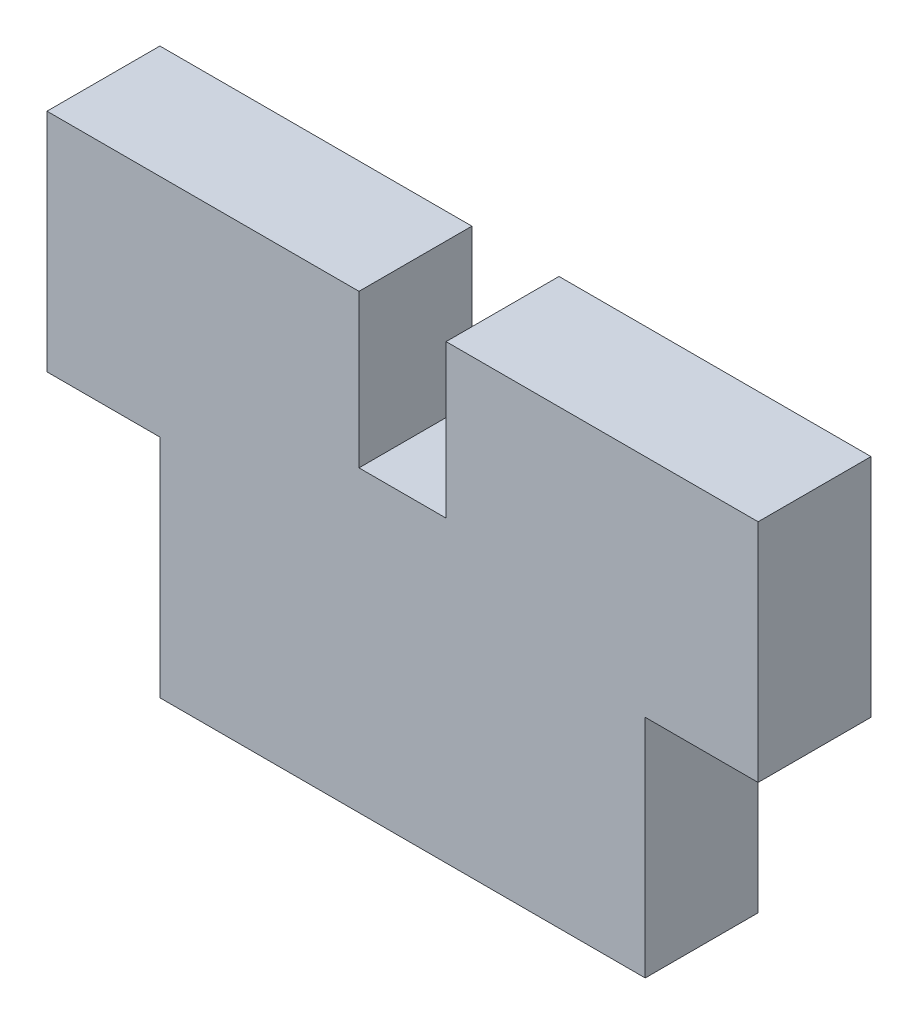
SolidWorks part; units mm, degrees
material "Acrylic (Medium-high impact)"
ref_plane "Front Plane" through (0, 0, 0) normal (0, 0, 1) x (1, 0, 0)
ref_plane "Top Plane" through (0, 0, 0) normal (0, 1, 0) x (1, 0, 0)
ref_plane "Right Plane" through (0, 0, 0) normal (1, 0, 0) x (0, 0, -1)
sketch "Sketch2" plane through (0, 0, 0) normal (0, 0, 1) x (1, 0, 0)
  line L1 (-20, -6.35) -> (20, -6.35)
  line L2 (-20, -6.35) -> (-20, 6.35)
  line L3 (-20, 6.35) -> (20, 6.35)
  line L4 (20, -6.35) -> (20, 6.35)
  line L5 (-20, -6.35) -> (20, 6.35) construction
  line L6 (-20, 6.35) -> (20, -6.35) construction
  point P0 (0, 0)
  dimension "D1" = 12.7
  dimension "D2" = 40
extrude "Boss-Extrude1" add sketch "Sketch2" along normal blind 6.35
sketch "Sketch3" plane through (0, -6.35, 0) normal (0, -1, 0) x (1, 0, 0)
  line L0 (-20, 6.35) -> (20, 6.35) construction
  line L1 (-13.65, 0) -> (13.65, 0)
  line L2 (-13.65, 0) -> (-13.65, 6.35)
  line L3 (-13.65, 6.35) -> (13.65, 6.35)
  line L4 (13.65, 0) -> (13.65, 6.35)
  line L5 (-13.65, 0) -> (13.65, 6.35) construction
  line L6 (-13.65, 6.35) -> (13.65, 0) construction
  line L7 (-20, 0) -> (20, 0) construction
  line L8 (20, 6.35) -> (20, 0) construction
  line L9 (-20, 6.35) -> (-20, 0) construction
  point P0 (0, 3.175)
  dimension "D1" = 0
  dimension "D2" = 0
  dimension "D3" = 6.35
  dimension "D4" = 6.35
extrude "Boss-Extrude2" add sketch "Sketch3" along normal blind 12.7
sketch "Sketch4" plane through (0, 6.35, 0) normal (0, 1, 0) x (1, 0, 0)
  line L0 (20, 0) -> (-20, 0) construction
  line L1 (-2.45, -6.35) -> (2.45, -6.35)
  line L2 (-2.45, -6.35) -> (-2.45, 0)
  line L3 (-2.45, 0) -> (2.45, 0)
  line L4 (2.45, -6.35) -> (2.45, 0)
  line L5 (-2.45, -6.35) -> (2.45, 0) construction
  line L6 (-2.45, 0) -> (2.45, -6.35) construction
  line L7 (20, -6.35) -> (-20, -6.35) construction
  line L8 (20, -6.35) -> (20, 0) construction
  point P0 (0, -3.175)
  dimension "D1" = 0
  dimension "D2" = 0
  dimension "D3" = 4.9
  dimension "D4" = 20
extrude "Cut-Extrude1" cut sketch "Sketch4" against normal blind 8.6
